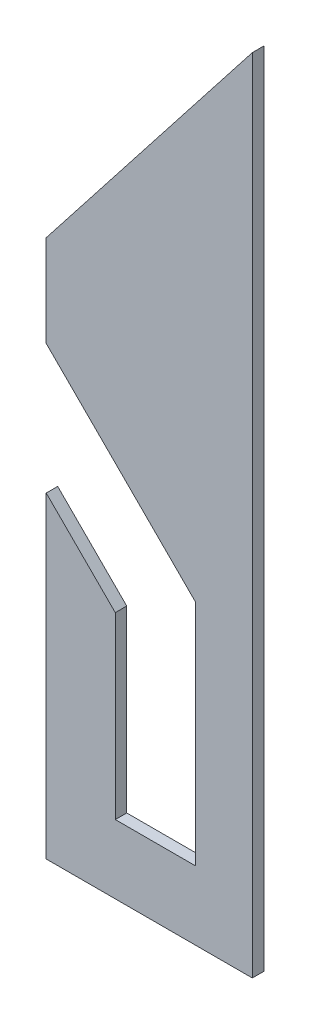
SolidWorks part; units mm, degrees
ref_plane "Front" through (0, 0, 0) normal (0, 0, 1) x (1, 0, 0)
ref_plane "Top" through (0, 0, 0) normal (0, 1, 0) x (1, 0, 0)
ref_plane "Right" through (0, 0, 0) normal (1, 0, 0) x (0, 0, -1)
sketch "Sketch1" plane through (0, 0, 0) normal (0, 0, 1) x (1, 0, 0)
  line L0 (90, 350) -> (0, 235)
  line L1 (0, 0) -> (90, 0)
  line L2 (0, 0) -> (0, 138.4315)
  line L4 (90, 0) -> (90, 350)
  line L5 (0, 138.4315) -> (30.159, 108.2725)
  line L14 (30.159, 108.2725) -> (30.159, 30)
  line L15 (30.159, 30) -> (65.159, 30)
  line L16 (65.159, 30) -> (65.159, 129.841)
  line L17 (65.159, 129.841) -> (0, 195)
  line L18 (0, 195) -> (0, 235)
  point P7 (32.5795, 162.4205)
  point P12 (65.159, 79.9205)
  point P16 (45, 0)
  dimension "D1" = 350
  dimension "D2" = 90
  dimension "D3" = 115
  dimension "D4" = 40
  dimension "D5" = 35
  dimension "D6" = 40
  dimension "D7" = 45
  dimension "D8" = 30
extrude "Boss-Extrude1" add sketch "Sketch1" along normal blind 5
